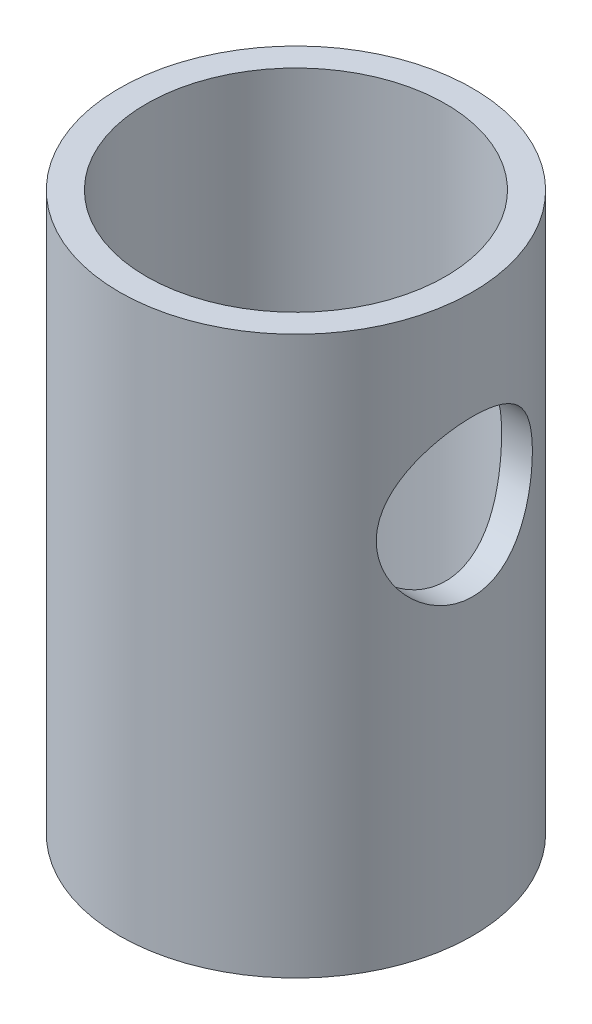
SolidWorks part; units mm, degrees
material "AISI 316 Stainless Steel Sheet (SS)"
ref_plane "Front Plane" through (0, 0, 0) normal (0, 0, 1) x (1, 0, 0)
ref_plane "Top Plane" through (0, 0, 0) normal (0, 1, 0) x (1, 0, 0)
ref_plane "Right Plane" through (0, 0, 0) normal (1, 0, 0) x (0, 0, -1)
sketch "Sketch1" plane through (0, 0, 0) normal (0, 1, 0) x (1, 0, 0)
  circle A0 centre (0, 0) radius 20.447
  circle A1 centre (0, 0) radius 24.13
  dimension "D1" = 3.683
  dimension "D2" = 48.26
extrude "Boss-Extrude1" add sketch "Sketch1" along normal blind 76.2
sketch "Sketch2" plane through (0, 0, 0) normal (1, 0, 0) x (0, 0, -1)
  line L0 (24.13, 76.2) -> (-24.13, 76.2) construction
  line L1 (0, 50.8) -> (0, 0) construction
  circle A0 centre (0, 50.8) radius 10.668
  dimension "D1" = 21.336
  dimension "D2" = 25.4
extrude "Cut-Extrude1" cut sketch "Sketch2" along normal blind 76.2
